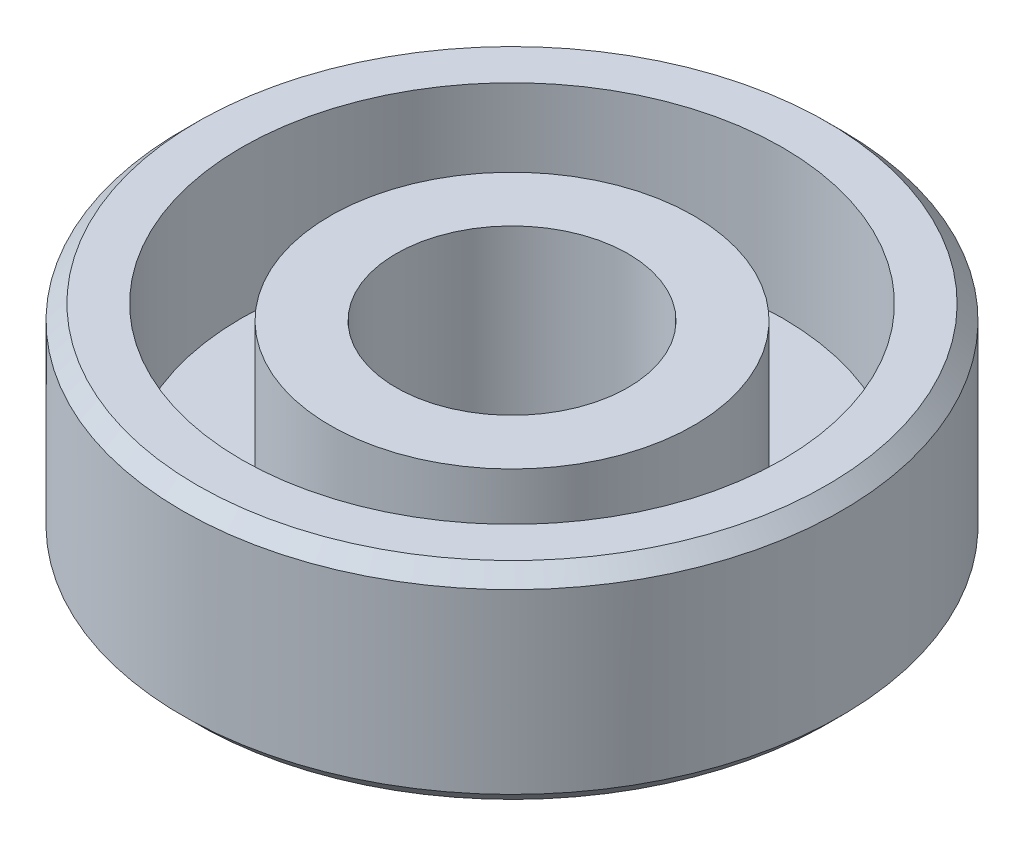
SolidWorks part; units mm, degrees
ref_plane "Front Plane" through (0, 0, 0) normal (0, 0, 1) x (1, 0, 0)
ref_plane "Top Plane" through (0, 0, 0) normal (0, 1, 0) x (1, 0, 0)
ref_plane "Right Plane" through (0, 0, 0) normal (1, 0, 0) x (0, 0, -1)
sketch "Sketch1" plane through (0, 0, 0) normal (0, 0, 1) x (1, 0, 0)
  line L0 (0, 0) -> (0, 26.7113) construction
  line L2 (3.925, 17.5925) -> (6.15, 17.5925)
  line L3 (3.925, 17.5925) -> (3.925, 11.0925)
  line L4 (3.925, 11.0925) -> (9.6628, 11.0925)
  line L5 (6.15, 17.5925) -> (6.15, 13.0925)
  line L6 (9.6628, 11.0925) -> (11.15, 11.0925)
  line L8 (6.15, 13.0925) -> (9.15, 13.0925)
  line L11 (9.15, 13.0925) -> (9.15, 18.0925)
  line L12 (9.15, 18.0925) -> (11.15, 18.0925)
  line L13 (11.15, 11.0925) -> (11.15, 18.0925)
  dimension "D1" = 7.85
  dimension "D2" = 3
  dimension "D3" = 2
  dimension "D4" = 22.3
  dimension "D5" = 7
  dimension "D6" = 0.5
  dimension "D7" = 2
revolve "Revolve1" add sketch "Sketch1" angle 360 about L0
chamfer "Chamfer1" distance 0.5 angle 45 2 edges at (0, 11.0925, -11.15) (0, 18.0925, -11.15)
